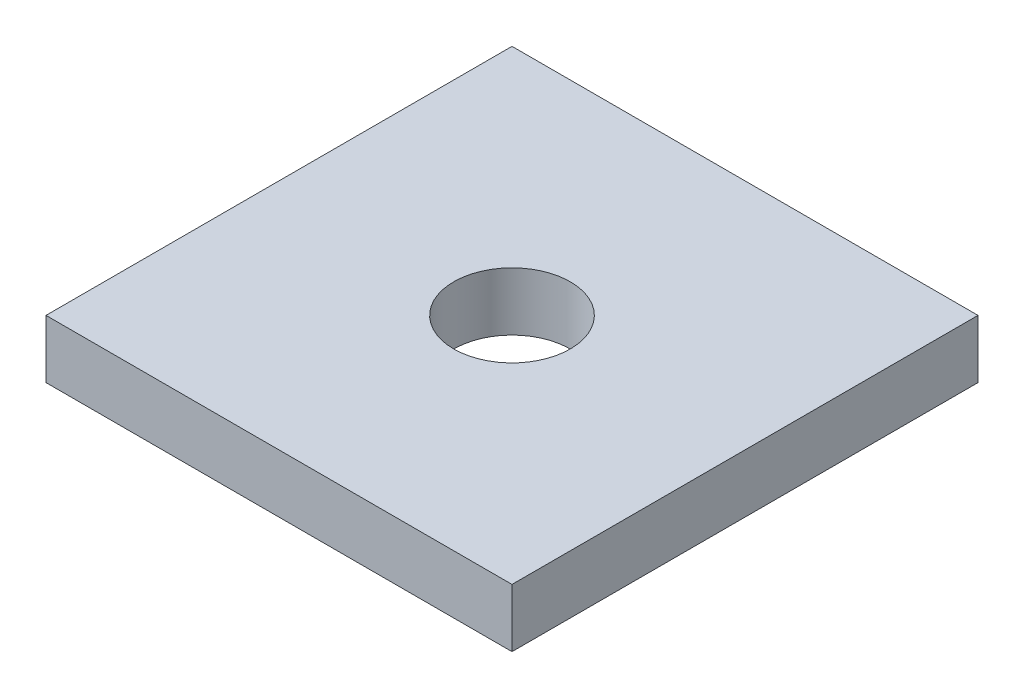
SolidWorks part; units mm, degrees
material "Plain Carbon Steel"
ref_plane "Front Plane" through (0, 0, 0) normal (0, 0, 1) x (1, 0, 0)
ref_plane "Top Plane" through (0, 0, 0) normal (0, 1, 0) x (1, 0, 0)
ref_plane "Right Plane" through (0, 0, 0) normal (1, 0, 0) x (0, 0, -1)
sketch "Sketch1" plane through (0, 0, 0) normal (0, 1, 0) x (1, 0, 0)
  line L1 (25.4, 25.4) -> (-25.4, 25.4)
  line L2 (25.4, 25.4) -> (25.4, -25.4)
  line L3 (25.4, -25.4) -> (-25.4, -25.4)
  line L4 (-25.4, 25.4) -> (-25.4, -25.4)
  line L5 (25.4, 25.4) -> (-25.4, -25.4) construction
  line L6 (25.4, -25.4) -> (-25.4, 25.4) construction
  circle A0 centre (0, 0) radius 6.35
  point P0 (0, 0)
  dimension "D3" = 12.7
  dimension "D1" = 50.8
  dimension "D2" = 50.8
extrude "Boss-Extrude1" add sketch "Sketch1" along normal blind 6.35
